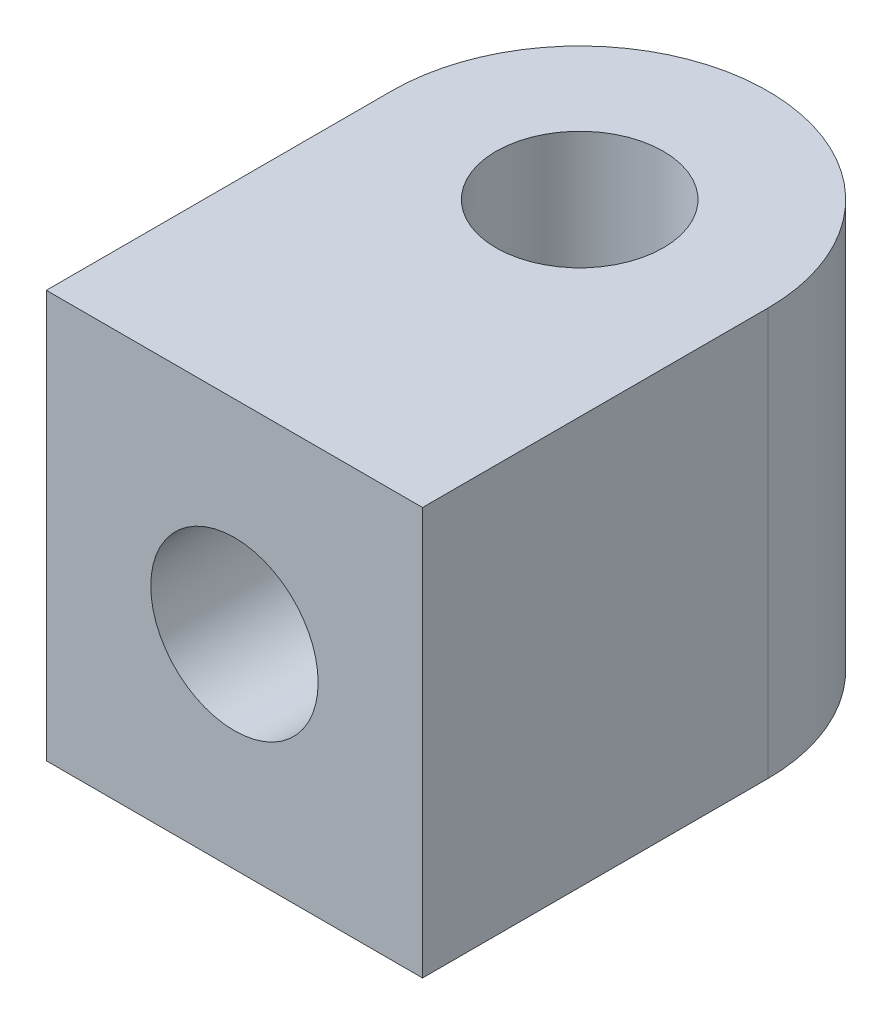
SolidWorks part; units mm, degrees
ref_plane "Front Plane" through (0, 0, 0) normal (0, 0, 1) x (1, 0, 0)
ref_plane "Top Plane" through (0, 0, 0) normal (0, 1, 0) x (1, 0, 0)
ref_plane "Right Plane" through (0, 0, 0) normal (1, 0, 0) x (0, 0, -1)
ref_plane "Plane1" through (0, 0, 0) normal (0, -1, 0) x (1, 0, 0)
sketch "Sketch1" plane through (0, 0, 0) normal (0, -1, 0) x (1, 0, 0)
  line L0 (3.0404, 0) -> (3.0404, 5.5804)
  line L1 (3.0404, 5.5804) -> (-3.0404, 5.5804)
  line L2 (-3.0404, 5.5804) -> (-3.0404, 0)
  arc A0 (-3.0404, 0) -> (3.0404, 0) centre (0, 0) ccw
extrude "Boss-Extrude1" add sketch "Sketch1" against normal blind 6.5862
hole_wizard "M2.5 Clearance Hole1" positions "Sketch3" profile "Sketch2" hole size "M2.5" standard "ANSI Metric"
sketch "Sketch3" plane through (0, 0, 0) normal (0, -1, 0) x (-1, 0, 0)
  point P0 (0, 0)
sketch "Sketch2" plane through (0, 0, 0) normal (1, 0, 0) x (0, 0, -1)
  line L0 (0, 0) -> (0, 6.5862)
  line L1 (0, 6.5862) -> (1.3525, 6.5862)
  line L2 (1.3525, 6.5862) -> (1.3525, 0)
  line L5 (1.3525, 0) -> (0, 0)
  line L11 (0, -6.35) -> (0, 107.95) construction
  dimension "Thru Hole Dia." = 2.7051
  dimension "Thru Hole Depth" = 6.5862
hole_wizard "M2.5 Clearance Hole2" positions "Sketch5" profile "Sketch4" hole size "M2.5" standard "ANSI Metric"
sketch "Sketch5" plane through (0, 0, 5.5804) normal (0, 0, 1) x (1, 0, 0)
  point P0 (0, 3.2931)
sketch "Sketch4" plane through (0, 3.2931, 5.5804) normal (1, 0, 0) x (0, -1, 0)
  line L0 (0, 0) -> (0, 4.2278)
  line L1 (0, 4.2278) -> (1.3525, 4.2278)
  line L2 (1.3525, 4.2278) -> (1.3525, 0)
  line L5 (1.3525, 0) -> (0, 0)
  line L11 (0, -6.35) -> (0, 107.95) construction
  dimension "Thru Hole Dia." = 2.7051
  dimension "Thru Hole Depth" = 4.2278
